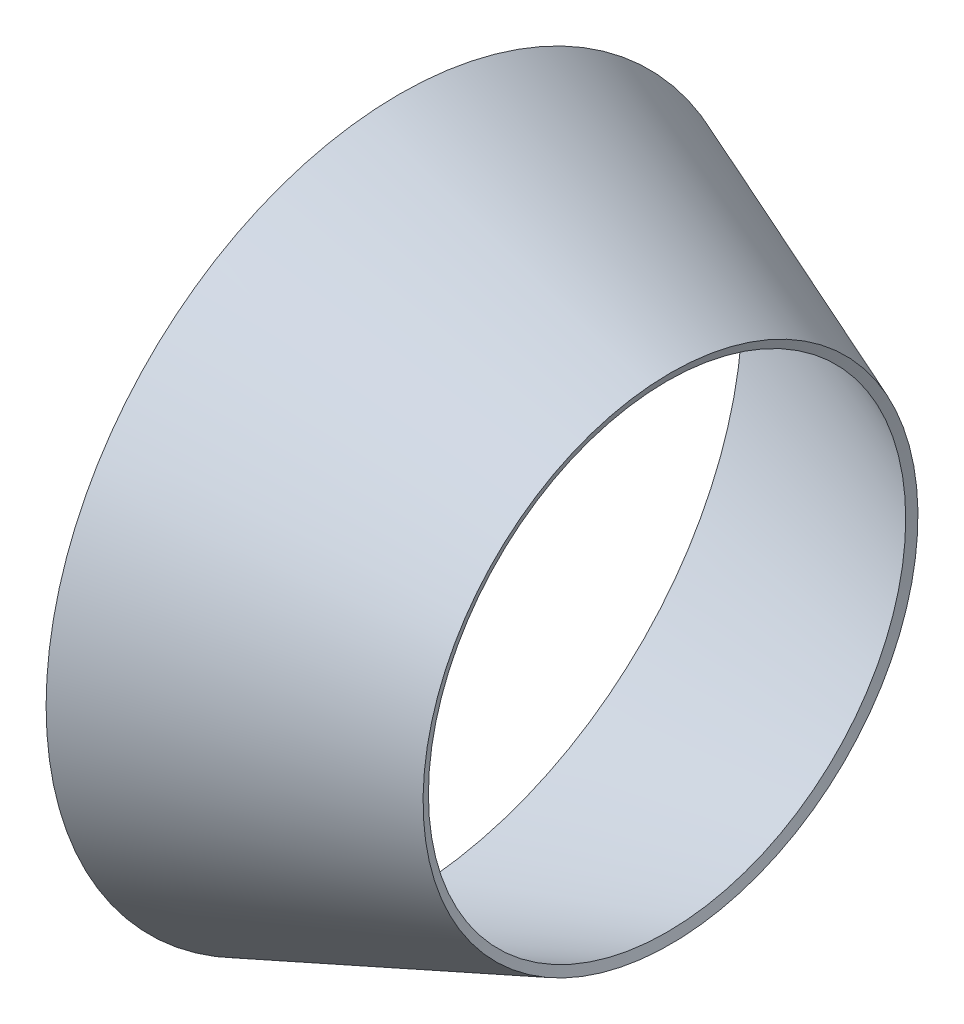
SolidWorks part; units mm, degrees
ref_plane "Front Plane" through (0, 0, 0) normal (0, 0, 1) x (1, 0, 0)
ref_plane "Top Plane" through (0, 0, 0) normal (0, 1, 0) x (1, 0, 0)
ref_plane "Right Plane" through (0, 0, 0) normal (1, 0, 0) x (0, 0, -1)
sketch "Sketch1" plane through (0, 0, 0) normal (0, 0, 1) x (1, 0, 0)
  line L0 (-42.0913, -47.5161) -> (-5.626, -33.2811)
  line L1 (-42.0913, -47.5161) -> (-42.0913, 47.5161) construction
  line L2 (-5.626, -33.2811) -> (-6.0878, -32.098)
  line L3 (-6.0878, -32.098) -> (-42.0913, -46.1527)
  line L4 (-42.0913, -45.72) -> (-42.0913, 45.72) construction
  line L5 (0, 0) -> (-88.1772, 0) construction
  line L6 (-129.4673, 0) -> (-46.8871, 0) construction
  line L7 (-42.0913, -47.5161) -> (-42.0913, -46.1527)
  dimension "D1" = 1.27
revolve "Revolve1" add sketch "Sketch1" angle 360 about L5
